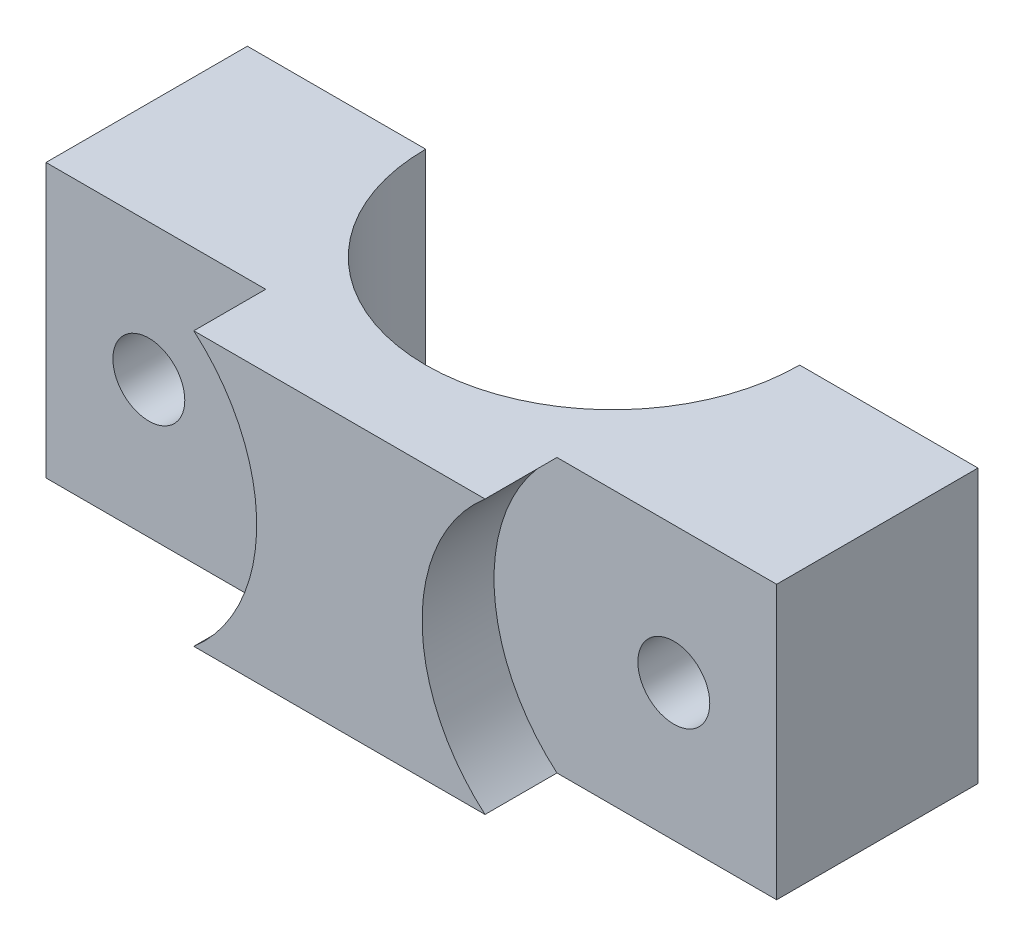
SolidWorks part; units mm, degrees
ref_plane "Front Plane" through (0, 0, 0) normal (0, 0, 1) x (1, 0, 0)
ref_plane "Top Plane" through (0, 0, 0) normal (0, 1, 0) x (1, 0, 0)
ref_plane "Right Plane" through (0, 0, 0) normal (1, 0, 0) x (0, 0, -1)
sketch "Sketch2" plane through (0, 0, 0) normal (0, 0, 1) x (1, 0, 0)
  line L1 (-25.4, 9.5) -> (25.4, 9.5)
  line L2 (-25.4, 9.5) -> (-25.4, -9.5)
  line L3 (-25.4, -9.5) -> (25.4, -9.5)
  line L4 (25.4, 9.5) -> (25.4, -9.5)
  line L5 (-25.4, 9.5) -> (25.4, -9.5) construction
  line L6 (-25.4, -9.5) -> (25.4, 9.5) construction
  point P0 (0, 0)
  dimension "D1" = 50.8
  dimension "D2" = 19
extrude "Boss-Extrude1" add sketch "Sketch2" along normal blind 19
sketch "Sketch3" plane through (0, -9.5, 0) normal (0, -1, 0) x (1, 0, 0)
  circle A0 centre (0, 0) radius 13
extrude "Cut-Extrude1" cut sketch "Sketch3" against normal through all
sketch "Sketch4" plane through (0, 0, 19) normal (0, 0, 1) x (1, 0, 0)
  line L0 (0, 0) -> (0, -7.1376) construction
  circle A0 centre (-18.25, 0) radius 2.5
  circle A1 centre (-18.25, 0) radius 12.5
  circle A2 centre (18.25, 0) radius 12.5
  circle A3 centre (18.25, 0) radius 2.5
  line M4 (25.4, -9.5) -> (25.4, 9.5)
  line M5 (25.4, 9.5) -> (-25.4, 9.5)
  line M6 (-25.4, 9.5) -> (-25.4, -9.5)
  line M7 (-25.4, -9.5) -> (25.4, -9.5)
  dimension "D1" = 18.25
extrude "Cut-Extrude2" cut sketch "Sketch4" against normal blind 5 contours A1 A0 M7 M5 M6 | A2 A3 M7 M4 M5
sketch "Sketch5" plane through (0, 0, 19) normal (0, 0, 1) x (1, 0, 0)
  circle A1 centre (18.25, 0) radius 2.5
  circle A2 centre (18.25, 0) radius 2.5
  circle A3 centre (-18.25, 0) radius 2.5
  circle A4 centre (-18.25, 0) radius 2.5
  dimension "D1" = 0
  dimension "D2" = 0
extrude "Cut-Extrude3" cut sketch "Sketch5" against normal through all both and the other way through all
